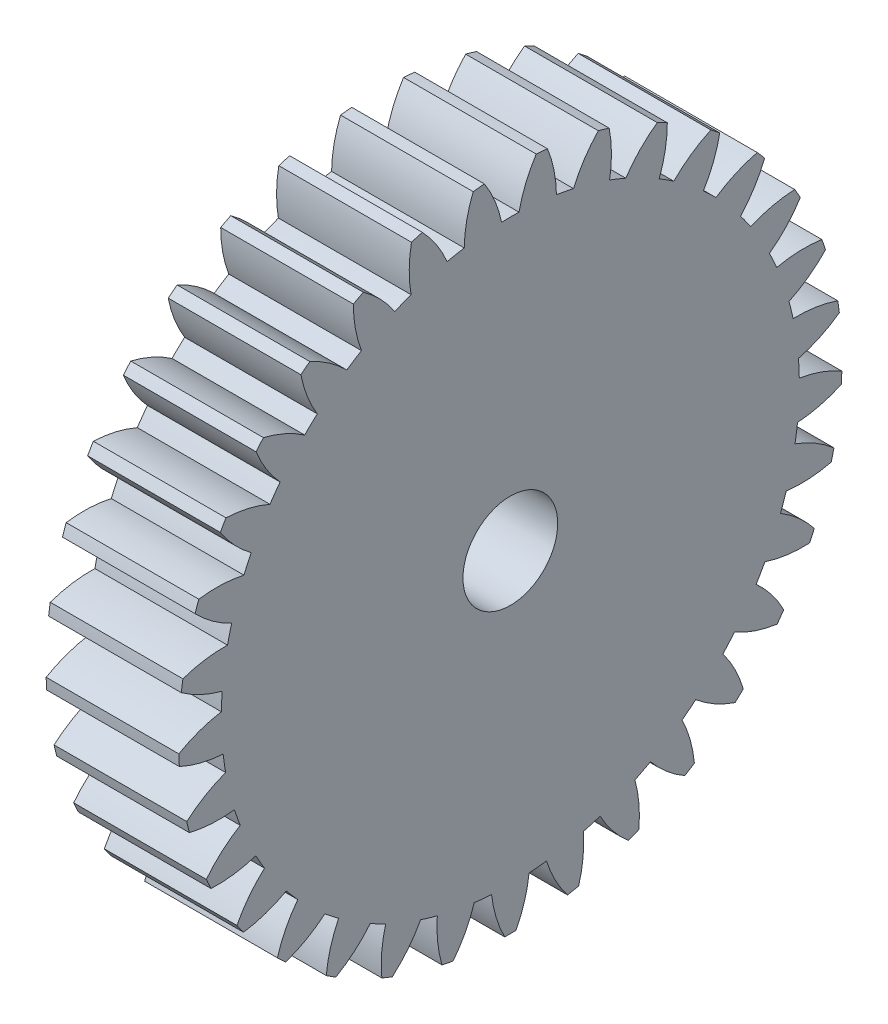
SolidWorks part; units mm, degrees
ref_plane "Plane1" through (0, 0, 0) normal (0, 0, 1) x (1, 0, 0)
ref_plane "Plane2" through (0, 0, 0) normal (0, 1, 0) x (1, 0, 0)
ref_plane "Plane3" through (0, 0, 0) normal (1, 0, 0) x (0, 0, -1)
sketch "HoldingSke" plane through (0, 0, 0) normal (0, 1, 0) x (1, 0, 0)
  line L0 (0, 0) -> (0.8387, -0.5446)
  line L1 (-15, 0) -> (100, 0) construction
  line L2 (0, 0) -> (-2.1039, 2.3779)
  line L3 (0, 0) -> (-11.863, 4.5341)
  line L4 (0, 0) -> (7.2428, 4.7035)
  line L5 (0, 0) -> (-46.8476, -17.4728)
  line L6 (0, 0) -> (-9.9476, -6.7116)
  line L7 (-2.1039, 2.3779) -> (8.6586, 51.2059)
  line L8 (-76.2, 54.61) -> (-75.3, 54.61)
  line L9 (-71.009, 38.7566) -> (-53.1078, 45.2721)
  line L10 (-76.2, 71.12) -> (104.1128, 71.12)
  line L11 (0, 0) -> (-12, 0)
  line L12 (-76.2, 101.6) -> (-76.162, 101.6)
  line L13 (24.9733, 27.94) -> (52.9518, 28.4284)
  line L14 (24.9733, 27.94) -> (24.9743, 27.94)
  line L15 (24.9733, 27.94) -> (100.4006, 29.5858)
  line L16 (-63.627, -1) -> (-12.827, -1)
  circle A0 centre (0, 0) radius 2.5
  circle A1 centre (0, 0) radius 15.249
  circle A2 centre (0, 0) radius 37.5
  circle A3 centre (0, 0) radius 2.5
  dimension "MHD" = 30.498
  dimension "Hub_dia" = 75
  dimension "Bore" = 5
  dimension "MBD" = 5
  dimension "Num_teeth" = 33
  dimension "Pitch" = 1
  dimension "Overall_len" = 50
  dimension "Show_teeth" = 33
  dimension "Thickness" = 12
  dimension "OAL" = 50.0001
  dimension "T_dim" = 0.9
  dimension "Ap" = 20
  dimension "H" = 19.05
  dimension "Pitch_radius" = 180.3128
  dimension "Width" = 12
  dimension "Backlash" = 0.038
  dimension "Addendum_fac" = 1
  dimension "Dedendum_fac" = 1.25
  dimension "Clearance_fac" = 0.25
  dimension "Dedendum_add" = 0.001
  dimension "Module" = 1
sketch "BasProSke" plane through (0, 0, 0) normal (0, 1, 0) x (1, 0, 0)
  line L0 (-10, 0) -> (60, 0) construction
  line L1 (0, 0) -> (0, 17.5)
  line L2 (0, 0) -> (7, 0)
  line L3 (7, 0) -> (7, 17.5)
  line L4 (7, 17.5) -> (0, 17.5)
  dimension "Thickness" = 7
  dimension "Diameter" = 35
revolve "Base-Revolve" add sketch "BasProSke" angle 360 about L0
sketch "TooCutSke" plane through (0, 0, 0) normal (1, 0, 0) x (0, 0, -1)
  line L1 (0, 0) -> (0, 107) construction
  line L2 (0, 0) -> (-0.8516, 16.478) construction
  line L3 (0, 0) -> (-3.1339, 32.8194) construction
  line L4 (-0.8516, 16.478) -> (-1.5669, 16.4097) construction
  arc A0 (0.46, 15.2421) -> (-0.46, 15.2421) centre (0, 0) ccw
  arc A1 (1.3819, 17.4708) -> (-1.3819, 17.4708) centre (0, 0) ccw
  circle A2 centre (0, 0) radius 16.5 construction
  circle A3 centre (0, 0) radius 15.5049 construction
  arc A4 (-0.46, 15.2421) -> (-1.3819, 17.4708) centre (-6.9172, 13.8764) ccw
  arc A5 (1.3819, 17.4708) -> (0.46, 15.2421) centre (6.9172, 13.8764) ccw
  dimension "Root_dia" = 30.498
  dimension "Overcut_dia" = 35.0508
  dimension "Pitch_dia" = 33
  dimension "Base_dia" = 31.0099
  dimension "Flank_rad" = 6.6
  dimension "Half_ang" = 5.455
  dimension "Half_CT" = 0.7186
extrude "ToothCut" cut sketch "TooCutSke" along normal through all
fillet "Breaks" [suppressed] radius 0.02
fillet "RootFillets" [suppressed] radius 0.251
pattern_circular "TeethCuts" count 33 every 10.909 about axis through (-10, 0, 0) along (1, 0, 0) of "ToothCut", "RootFillets", "Breaks"
sketch "HubNeaOneSke" plane through (0, 0, 0) normal (-1, 0, 0) x (0, 0, 1)
  circle A0 centre (0, 0) radius 15.249
  dimension "Diameter" = 30.498
extrude "HubNearOne" [suppressed] add sketch "HubNeaOneSke" along normal blind 43.0001
sketch "HubNeaBotSke" plane through (0, 0, 0) normal (-1, 0, 0) x (0, 0, 1)
  circle A0 centre (0, 0) radius 15.249
  dimension "Diameter" = 30.498
extrude "HubNearBoth" [suppressed] add sketch "HubNeaBotSke" along normal blind 21.5
ref_plane "FarPln" through (7, 0, 0) normal (1, 0, 0) x (0, 0, -1)
sketch "HubFarSke" plane through (7, 0, 0) normal (1, 0, 0) x (0, 0, -1)
  circle A0 centre (0, 0) radius 15.249
  dimension "Diameter" = 30.498
extrude "HubFar" [suppressed] add sketch "HubFarSke" along normal blind 21.5
sketch "BorSke" plane through (0, 0, 0) normal (1, 0, 0) x (0, 0, -1)
  circle A0 centre (0, 0) radius 2.5
  dimension "Diameter" = 5
extrude "Bore" cut sketch "BorSke" along normal mid plane 100.0001
sketch "KeySke" plane through (0, 0, 0) normal (1, 0, 0) x (0, 0, -1)
  line L0 (-1, 0) -> (-1, 3.4)
  line L1 (-1, 3.4) -> (1, 3.4)
  line L2 (1, 3.4) -> (1, 0)
  line L3 (0, 0) -> (0, 34) construction
  line L4 (-1, 0) -> (1, 0)
  dimension "Offset" = 3.4
  dimension "Width" = 2
extrude "Keyway" [suppressed] cut sketch "KeySke" along normal mid plane 100.0001
pattern_circular "Keyway2" [suppressed] count 2 every 90 about axis through (-10, 0, 0) along (1, 0, 0)
equation "' \"Module@HoldingSke\" = 6.35"
equation "' \"Num_teeth@HoldingSke\" = 12"
equation "' \"Ap@HoldingSke\" =  20"
equation "' \"Ap@HoldingSke\" = 20"
equation "' \"Width@HoldingSke\" = 0.5 * 25.4"
equation "' \"Hub_dia@HoldingSke\"= 1 * 25.4"
equation "' \"Hub_dia@HoldingSke\" = 1 * 25.4"
equation "' \"Overall_len@HoldingSke\" = 1.0 * 25.4"
equation "' \"Bore@HoldingSke\" = 0.75 * 25.4"
equation "' \"T_dim@HoldingSke\" = 0.1 * 25.4"
equation "' \"Width@KeySke\" = 0.25 * 25.4"
equation "' \"Show_teeth@HoldingSke\" = 13"
equation "' \"Backlash@HoldingSke\" = 0.009 * 25.4"
equation "' \"Addendum_fac@HoldingSke\" = 1.0"
equation "' \"Dedendum_fac@HoldingSke\" = 1.25"
equation "' \"Dedendum_add@HoldingSke\" = 0.00005 * 25.4"
equation "' \"Clearance_fac@HoldingSke\" = 0.25"
equation "\"Pitch@HoldingSke\" = 1 / \"Module@HoldingSke\""
equation "\"Overcut_dia@TooCutSke\" = (\"Num_teeth@HoldingSke\" + 2 * \"Addendum_fac@HoldingSke\") / \"Pitch@HoldingSke\" + 0.002 * 25.4"
equation "\"Pitch_dia@TooCutSke\" = \"Num_teeth@HoldingSke\" / \"Pitch@HoldingSke\""
equation "\"Base_dia@TooCutSke\" = \"Num_teeth@HoldingSke\" / \"Pitch@HoldingSke\" * cos((\"Ap@HoldingSke\"  * 3.14159265 / 180))"
equation "\"Root_dia@TooCutSke\" = (\"Num_teeth@HoldingSke\" + 2) / \"Pitch@HoldingSke\" - 2 * (\"Addendum_fac@HoldingSke\" + \"Dedendum_fac@HoldingSke\") / \"Pitch@HoldingSke\" - \"Dedendum_add@HoldingSke\" * 2"
equation "\"Half_ang@TooCutSke\" = 180 / \"Num_teeth@HoldingSke\""
equation "\"Half_CT@TooCutSke\" = \"Num_teeth@HoldingSke\" / \"Pitch@HoldingSke\" * sin((3.14159265 / 2 / \"Num_teeth@HoldingSke\")) / 2 - 7 * \"Backlash@HoldingSke\" / 4"
equation "\"Flank_rad@TooCutSke\" = \"Num_teeth@HoldingSke\" / \"Pitch@HoldingSke\" / 5"
equation "\"Radius@RootFillets\" = \"Clearance_fac@HoldingSke\" / \"Pitch@HoldingSke\" + \"Dedendum_add@HoldingSke\""
equation "\"Break_rad@Breaks\" = 0.02 / \"Pitch@HoldingSke\""
equation "\"Thickness@HoldingSke\" = \"Width@HoldingSke\""
equation "\"OAL@HoldingSke\" = \"Thickness@HoldingSke\""
equation "\"MHD@HoldingSke\" = (\"Num_teeth@HoldingSke\" + 2) / \"Pitch@HoldingSke\" - 2 * (\"Addendum_fac@HoldingSke\" + \"Dedendum_fac@HoldingSke\")  / \"Pitch@HoldingSke\" - \"Dedendum_add@HoldingSke\" * 2"
equation "\"MBD@HoldingSke\" = (\"Num_teeth@HoldingSke\" + 2) / \"Pitch@HoldingSke\" - 2 * (\"Addendum_fac@HoldingSke\" + \"Dedendum_fac@HoldingSke\")  / \"Pitch@HoldingSke\" - \"Dedendum_add@HoldingSke\" * 2 - 0.002 * 25.4"
equation "\"MHD@HoldingSke\" = ((sgn( \"MHD@HoldingSke\" - \"Hub_dia@HoldingSke\" )-1)*( \"MHD@HoldingSke\" - \"Hub_dia@HoldingSke\" ))/-2+ \"Hub_dia@HoldingSke\""
equation "\"MBD@HoldingSke\" = ((sgn( \"MBD@HoldingSke\" - \"Bore@HoldingSke\" )-1)*( \"MBD@HoldingSke\" - \"Bore@HoldingSke\" ))/-2+ \"Bore@HoldingSke\""
equation "\"OAL@HoldingSke\" = ((sgn( \"OAL@HoldingSke\" - \"Overall_len@HoldingSke\" )+1)*( \"OAL@HoldingSke\" - \"Overall_len@HoldingSke\" ))/2 + \"Overall_len@HoldingSke\" + 0.000002 * 25.4"
equation "\"Num_teeth@TeethCuts\" = int( \"Show_teeth@HoldingSke\" ) + 1"
equation "\"Num_teeth@TeethCuts\" = ((sgn( \"Num_teeth@TeethCuts\" - \"Num_teeth@HoldingSke\" )-1)*( \"Num_teeth@TeethCuts\" - \"Num_teeth@HoldingSke\" ))/-2+ \"Num_teeth@HoldingSke\""
equation "\"Num_teeth@TeethCuts\" = ((sgn( \"Num_teeth@TeethCuts\" - 2.0)+1)*( \"Num_teeth@TeethCuts\" - 2.0))/2 +2.0"
equation "\"Angle@TeethCuts\" = 360.0 / \"Num_teeth@HoldingSke\""
equation "\"Diameter@BasProSke\" = (\"Num_teeth@HoldingSke\" + 2 * \"Addendum_fac@HoldingSke\") / \"Pitch@HoldingSke\""
equation "\"Thickness@BasProSke\"=\"Thickness@HoldingSke\"- (5mm)"
equation "' \"Fillet_rad@BasProSke\" =  \"Thickness@HoldingSke\" * 0.05"
equation "' \"Fillet_rad@BasProSke\" = \"Thickness@HoldingSke\" * 0.05"
equation "\"MHD@HoldingSke\" = ((sgn( \"MHD@HoldingSke\" - \"Root_dia@TooCutSke\" )-1)*( \"MHD@HoldingSke\" - \"Root_dia@TooCutSke\" ))/-2+ \"Root_dia@TooCutSke\""
equation "\"Diameter@HubNeaOneSke\" = \"MHD@HoldingSke\""
equation "\"Length@HubNearOne\" = \"OAL@HoldingSke\" - \"Thickness@BasProSke\""
equation "\"Diameter@HubNeaBotSke\" = \"MHD@HoldingSke\""
equation "\"Length@HubNearBoth\" = ( \"OAL@HoldingSke\" - \"Thickness@BasProSke\" ) / 2.0"
equation "\"Thickness@FarPln\" = \"Thickness@BasProSke\""
equation "\"Diameter@HubFarSke\" = \"MHD@HoldingSke\""
equation "\"Length@HubFar\" = ( \"OAL@HoldingSke\" - \"Thickness@BasProSke\" ) / 2.0"
equation "\"Diameter@BorSke\" = \"MBD@HoldingSke\""
equation "\"D1@Bore\" = \"OAL@HoldingSke\" * 2.0"
equation "\"D1@Keyway\" = \"OAL@HoldingSke\" * 2.0"
equation "\"Offset@KeySke\" = \"T_dim@HoldingSke\" + \"MBD@HoldingSke\" / 2.0"
